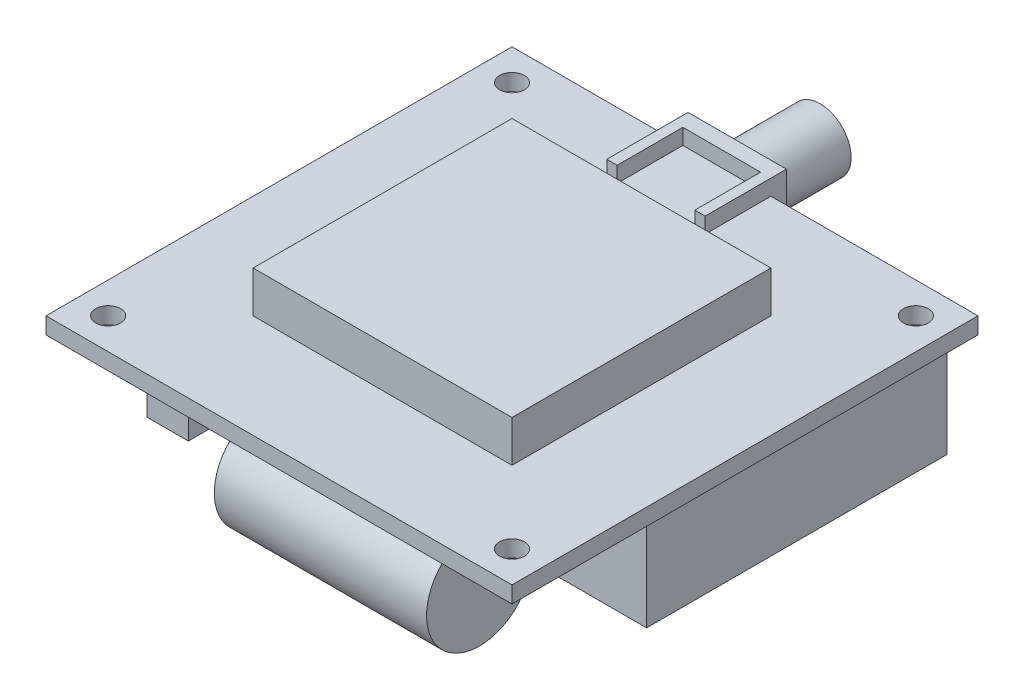
SolidWorks part; units mm, degrees
ref_plane "Front Plane" through (0, 0, 0) normal (0, 0, 1) x (1, 0, 0)
ref_plane "Top Plane" through (0, 0, 0) normal (0, 1, 0) x (1, 0, 0)
ref_plane "Right Plane" through (0, 0, 0) normal (1, 0, 0) x (0, 0, -1)
sketch "Sketch1" plane through (0, 0, 0) normal (0, 1, 0) x (1, 0, 0)
  line L1 (-22.5, -22.5) -> (22.5, -22.5)
  line L2 (-22.5, -22.5) -> (-22.5, 22.5)
  line L3 (-22.5, 22.5) -> (22.5, 22.5)
  line L4 (22.5, -22.5) -> (22.5, 22.5)
  line L5 (-22.5, -22.5) -> (22.5, 22.5) construction
  line L6 (-22.5, 22.5) -> (22.5, -22.5) construction
  point P0 (0, 0)
  dimension "D1" = 45
  dimension "D2" = 45
extrude "PCB" add sketch "Sketch1" along normal blind 1.6
hole_wizard "PCB mounting holes" positions "Sketch2" profile "Sketch3" hole size "M2" standard "ANSI Metric" end condition through all
sketch "Sketch2" plane through (0, 0, 0) normal (0, -1, 0) x (-1, 0, 0)
  line L1 (19.5, 19.5) -> (-19.5, 19.5) construction
  line L2 (19.5, 19.5) -> (19.5, -19.5) construction
  line L3 (19.5, -19.5) -> (-19.5, -19.5) construction
  line L4 (-19.5, 19.5) -> (-19.5, -19.5) construction
  line L5 (19.5, 19.5) -> (-19.5, -19.5) construction
  line L6 (19.5, -19.5) -> (-19.5, 19.5) construction
  point P2 (-19.5, -19.5)
  point P183 (19.5, 19.5)
  point P184 (19.5, -19.5)
  point P185 (-19.5, 19.5)
  point P196 (0, 0)
  dimension "D1" = 39
  dimension "D2" = 39
sketch "Sketch3" plane through (19.5, 0, 19.5) normal (1, 0, 0) x (0, 0, -1)
  line L0 (0, 0) -> (0, 1.6)
  line L1 (0, 1.6) -> (1.2, 1.6)
  line L2 (1.2, 1.6) -> (1.2, 0)
  line L5 (1.2, 0) -> (0, 0)
  line L11 (0, -6.35) -> (0, 107.95) construction
  dimension "Thru Hole Dia." = 2.4
  dimension "Thru Hole Depth" = 1.6
sketch "Sketch4" plane through (0, 0, 0) normal (0, -1, 0) x (1, 0, 0)
  line L0 (22.5, 22.5) -> (22.5, -22.5) construction
  line L1 (-10, 8) -> (21, 8)
  line L2 (-10, 8) -> (-10, -21)
  line L3 (-10, -21) -> (21, -21)
  line L4 (21, 8) -> (21, -21)
  line L5 (22.5, -22.5) -> (-22.5, -22.5) construction
  dimension "D1" = 31
  dimension "D2" = 29
  dimension "D3" = 1.5
  dimension "D4" = 1.5
extrude "Iridium Modem" add sketch "Sketch4" along normal blind 10
sketch "Sketch5" plane through (22.5, 0, 0) normal (1, 0, 0) x (0, 0, -1)
  line L0 (-22.5, 0) -> (22.5, 0) construction
  line L1 (-22.5, 1.6) -> (-22.5, 0) construction
  circle A0 centre (-17.4, -5.1) radius 5.1
  dimension "D1" = 10.2
extrude "Capacitor 1" add sketch "Sketch5" against normal blind 20.5 from offset 8.25 separate body offset against normal yes
sketch "Sketch6" plane through (0, 0, -22.5) normal (0, 0, -1) x (-1, 0, 0)
  line L0 (-22.5, 0) -> (22.5, 0) construction
  line L1 (22.5, 1.6) -> (22.5, 0) construction
  circle A0 centre (17.4, -5.1) radius 5.1
  dimension "D1" = 10.2
extrude "Capacitor 2" add sketch "Sketch6" against normal blind 20.5 from offset 1 separate body offset against normal yes
sketch "Sketch7" plane through (0, 0, -22.5) normal (0, 0, -1) x (-1, 0, 0)
  line L1 (7, 3.1151) -> (-2.5, 3.1151)
  line L2 (7, 3.1151) -> (7, -4.6849)
  line L3 (7, -4.6849) -> (-2.5, -4.6849)
  line L4 (-2.5, 3.1151) -> (-2.5, -4.6849)
  point P4 (-2.5, -0.7849)
  dimension "D1" = 9.5
  dimension "D2" = 7.8
  dimension "D3" = 20
extrude "Boss-Extrude5" add sketch "Sketch7" along normal blind 1.5
sketch "Sketch8" plane through (0, 0, -24) normal (0, 0, -1) x (-1, 0, 0)
  line L0 (7, 3.1151) -> (-2.5, -4.6849) construction
  circle A0 centre (2.25, -0.7849) radius 3
  dimension "D1" = 6
extrude "Boss-Extrude6" add sketch "Sketch8" along normal blind 8
sketch "Sketch9" plane through (0, 0, -22.5) normal (0, 0, 1) x (1, 0, 0)
  line L0 (2.5, 1.6) -> (-7, 1.6) construction
  line L1 (-7, 3.1151) -> (-6, 3.1151)
  line L2 (-7, 3.1151) -> (-7, 1.6)
  line L3 (-7, 1.6) -> (-6, 1.6)
  line L4 (-6, 3.1151) -> (-6, 1.6)
  line L6 (2.5, 3.1151) -> (1.5, 3.1151)
  line L7 (2.5, 3.1151) -> (2.5, 1.6)
  line L8 (2.5, 1.6) -> (1.5, 1.6)
  line L9 (1.5, 3.1151) -> (1.5, 1.6)
  dimension "D1" = 1
extrude "Boss-Extrude7" add sketch "Sketch9" along normal blind 6.35
sketch "Sketch10" plane through (0, 0, 0) normal (0, -1, 0) x (1, 0, 0)
  line L0 (-22.5, 22.5) -> (22.5, 22.5) construction
  line L1 (-11.75, 19.5) -> (-15.75, 19.5)
  line L2 (-11.75, 19.5) -> (-11.75, 1.7)
  line L3 (-11.75, 1.7) -> (-15.75, 1.7)
  line L4 (-15.75, 19.5) -> (-15.75, 1.7)
  line L5 (-22.5, -22.5) -> (-22.5, 22.5) construction
  dimension "D1" = 4
  dimension "D2" = 17.8
  dimension "D3" = 3
  dimension "D4" = 6.75
extrude "Molex picoblade 10 pos" add sketch "Sketch10" along normal blind 5
sketch "Sketch11" plane through (0, 1.6, 0) normal (0, 1, 0) x (1, 0, 0)
  line L0 (-7, 22.5) -> (-22.5, 22.5) construction
  line L1 (12.5, 12.5) -> (-12.5, 12.5)
  line L2 (12.5, 12.5) -> (12.5, -12.5)
  line L3 (12.5, -12.5) -> (-12.5, -12.5)
  line L4 (-12.5, 12.5) -> (-12.5, -12.5)
  line L5 (-22.5, 22.5) -> (-22.5, -22.5) construction
  dimension "D1" = 25
  dimension "D2" = 25
  dimension "D3" = 10
  dimension "D4" = 10
extrude "Antenna" add sketch "Sketch11" along normal blind 4
